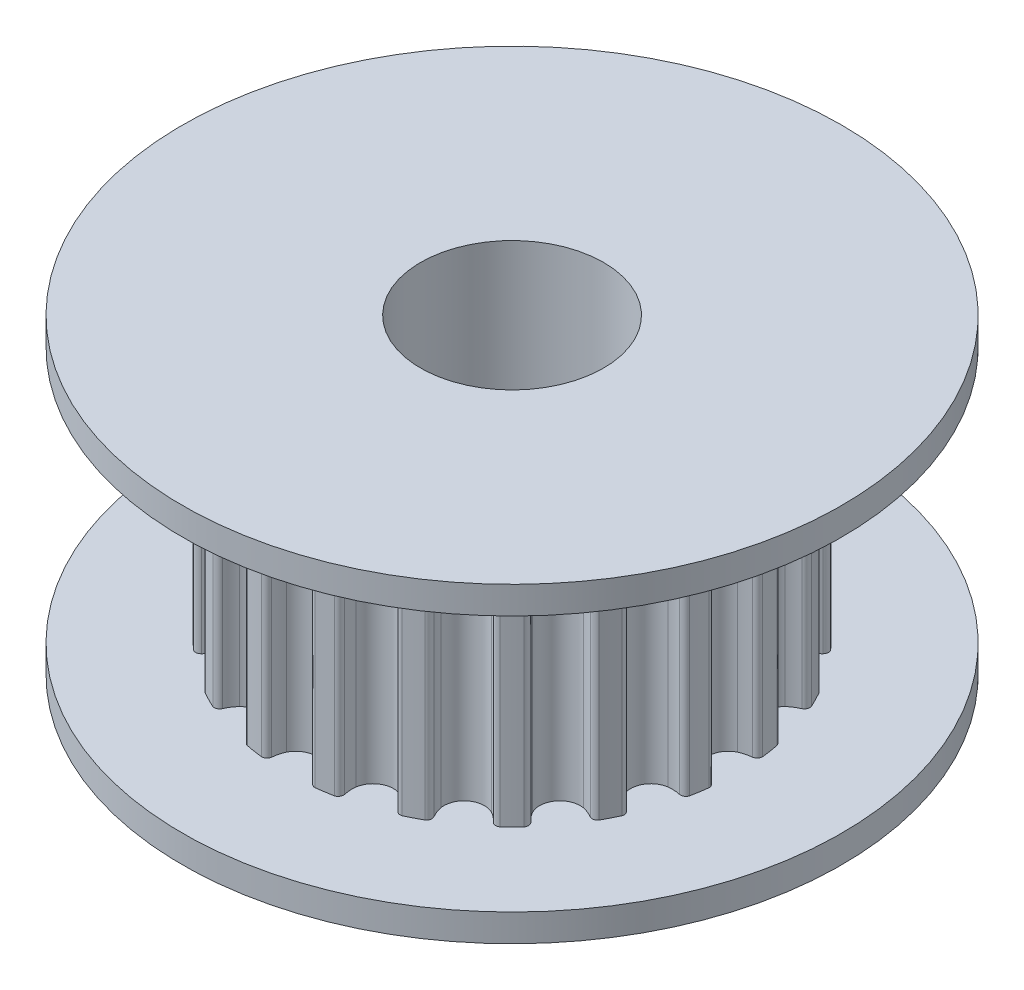
SolidWorks part; units mm, degrees
ref_plane "Front" through (0, 0, 0) normal (0, 0, 1) x (1, 0, 0)
ref_plane "Top" through (0, 0, 0) normal (0, 1, 0) x (1, 0, 0)
ref_plane "Right" through (0, 0, 0) normal (1, 0, 0) x (0, 0, -1)
sketch "Sketch1" plane through (0, 0, 0) normal (0, 0, 1) x (1, 0, 0)
  line L0 (0, 0) -> (0, 8.5) construction
  line L1 (2.5, 0) -> (2.5, 8.5)
  line L2 (2.5, 8.5) -> (9, 8.5)
  line L3 (9, 8.5) -> (9, 7.75)
  line L4 (9, 7.75) -> (6.3662, 7.75)
  line L5 (6.3662, 7.75) -> (6.3662, 0.75)
  line L6 (6.3662, 0.75) -> (9, 0.75)
  line L7 (9, 0.75) -> (9, 0)
  line L8 (9, 0) -> (2.5, 0)
  dimension "D1" = 8.5
  dimension "D2" = 7
  dimension "D3" = 18
  dimension "D4" = 12.7324
  dimension "D5" = 5
revolve "Revolve1" add sketch "Sketch1" angle 360 about L0
sketch "Sketch2" plane through (0, 0.75, 0) normal (0, 1, 0) x (1, 0, 0)
  circle A0 centre (0, 0) radius 6.3662 construction
  circle A1 centre (0, 0) radius 6.3662
  circle A3 centre (0, 0) radius 4.3662
  dimension "D1" = 2
extrude "Cut-Extrude1" cut sketch "Sketch2" along normal up to surface (7 mm away) up to face at (0, 7.75, -9)
sketch "Sketch3" plane through (0, 0.75, 0) normal (0, 1, 0) x (1, 0, 0)
  circle A0 centre (0, 0) radius 1.5
  arc A1 (6.1135, -0.7303) -> (5.9829, -0.5816) centre (5.9635, -0.7303) ccw
  arc A2 (5.659, -0.4964) -> (5.9829, -0.5816) centre (6.0717, 0.4144) ccw
  arc A3 (5.3522, 0) -> (5.659, -0.4964) centre (5.9072, 0) ccw
  arc A4 (5.659, 0.4964) -> (5.3522, 0) centre (5.9072, 0) ccw
  arc A5 (5.9829, 0.5816) -> (5.659, 0.4964) centre (6.0717, -0.4144) ccw
  arc A6 (5.9829, 0.5816) -> (6.1135, 0.7303) centre (5.9635, 0.7303) ccw
  arc A7 (6.1135, 0.7303) -> (6.0399, 1.1946) centre (0.0442, 0.007) ccw
  arc A8 (6.0399, 1.1946) -> (5.8698, 1.2957) centre (5.8973, 1.1482) ccw
  arc A9 (5.5354, 1.2766) -> (5.8698, 1.2957) centre (5.6465, 2.2704) ccw
  arc A10 (5.0902, 1.6539) -> (5.5354, 1.2766) centre (5.6181, 1.8254) ccw
  arc A11 (5.2286, 2.2208) -> (5.0902, 1.6539) centre (5.6181, 1.8254) ccw
  arc A12 (5.5103, 2.4019) -> (5.2286, 2.2208) centre (5.9026, 1.4821) ccw
  arc A13 (5.5103, 2.4019) -> (5.5886, 2.5838) centre (5.4459, 2.5374) ccw
  arc A14 (5.5886, 2.5838) -> (5.3752, 3.0025) centre (0.0399, 0.0203) ccw
  arc A15 (5.3752, 3.0025) -> (5.1821, 3.0461) centre (5.2538, 2.9144) ccw
  arc A16 (4.87, 2.9247) -> (5.1821, 3.0461) centre (4.6685, 3.9042) ccw
  arc A17 (4.33, 3.1459) -> (4.87, 2.9247) centre (4.779, 3.4722) ccw
  arc A18 (4.2864, 3.7279) -> (4.33, 3.1459) centre (4.779, 3.4722) ccw
  arc A19 (4.4984, 3.9872) -> (4.2864, 3.7279) centre (5.1557, 3.2336) ccw
  arc A20 (4.4984, 3.9872) -> (4.5166, 4.1843) centre (4.3953, 4.0961) ccw
  arc A21 (4.5166, 4.1843) -> (4.1843, 4.5166) centre (0.0317, 0.0317) ccw
  arc A22 (4.1843, 4.5166) -> (3.9872, 4.4984) centre (4.0961, 4.3953) ccw
  arc A23 (3.7279, 4.2864) -> (3.9872, 4.4984) centre (3.2336, 5.1557) ccw
  arc A24 (3.1459, 4.33) -> (3.7279, 4.2864) centre (3.4722, 4.779) ccw
  arc A25 (2.9247, 4.87) -> (3.1459, 4.33) centre (3.4722, 4.779) ccw
  arc A26 (3.0461, 5.1821) -> (2.9247, 4.87) centre (3.9042, 4.6685) ccw
  arc A27 (3.0461, 5.1821) -> (3.0025, 5.3752) centre (2.9144, 5.2538) ccw
  arc A28 (3.0025, 5.3752) -> (2.5838, 5.5886) centre (0.0203, 0.0399) ccw
  arc A29 (2.5838, 5.5886) -> (2.4019, 5.5103) centre (2.5374, 5.4459) ccw
  arc A30 (2.2208, 5.2286) -> (2.4019, 5.5103) centre (1.4821, 5.9026) ccw
  arc A31 (1.6539, 5.0902) -> (2.2208, 5.2286) centre (1.8254, 5.6181) ccw
  arc A32 (1.2766, 5.5354) -> (1.6539, 5.0902) centre (1.8254, 5.6181) ccw
  arc A33 (1.2957, 5.8698) -> (1.2766, 5.5354) centre (2.2704, 5.6465) ccw
  arc A34 (1.2957, 5.8698) -> (1.1946, 6.0399) centre (1.1482, 5.8973) ccw
  arc A35 (1.1946, 6.0399) -> (0.7303, 6.1135) centre (0.007, 0.0442) ccw
  arc A36 (0.7303, 6.1135) -> (0.5816, 5.9829) centre (0.7303, 5.9635) ccw
  arc A37 (0.4964, 5.659) -> (0.5816, 5.9829) centre (-0.4144, 6.0717) ccw
  arc A38 (0, 5.3522) -> (0.4964, 5.659) centre (0, 5.9072) ccw
  arc A39 (-0.4964, 5.659) -> (0, 5.3522) centre (0, 5.9072) ccw
  arc A40 (-0.5816, 5.9829) -> (-0.4964, 5.659) centre (0.4144, 6.0717) ccw
  arc A41 (-0.5816, 5.9829) -> (-0.7303, 6.1135) centre (-0.7303, 5.9635) ccw
  arc A42 (-0.7303, 6.1135) -> (-1.1946, 6.0399) centre (-0.007, 0.0442) ccw
  arc A43 (-1.1946, 6.0399) -> (-1.2957, 5.8698) centre (-1.1482, 5.8973) ccw
  arc A44 (-1.2766, 5.5354) -> (-1.2957, 5.8698) centre (-2.2704, 5.6465) ccw
  arc A45 (-1.6539, 5.0902) -> (-1.2766, 5.5354) centre (-1.8254, 5.6181) ccw
  arc A46 (-2.2208, 5.2286) -> (-1.6539, 5.0902) centre (-1.8254, 5.6181) ccw
  arc A47 (-2.4019, 5.5103) -> (-2.2208, 5.2286) centre (-1.4821, 5.9026) ccw
  arc A48 (-2.4019, 5.5103) -> (-2.5838, 5.5886) centre (-2.5374, 5.4459) ccw
  arc A49 (-2.5838, 5.5886) -> (-3.0025, 5.3752) centre (-0.0203, 0.0399) ccw
  arc A50 (-3.0025, 5.3752) -> (-3.0461, 5.1821) centre (-2.9144, 5.2538) ccw
  arc A51 (-2.9247, 4.87) -> (-3.0461, 5.1821) centre (-3.9042, 4.6685) ccw
  arc A52 (-3.1459, 4.33) -> (-2.9247, 4.87) centre (-3.4722, 4.779) ccw
  arc A53 (-3.7279, 4.2864) -> (-3.1459, 4.33) centre (-3.4722, 4.779) ccw
  arc A54 (-3.9872, 4.4984) -> (-3.7279, 4.2864) centre (-3.2336, 5.1557) ccw
  arc A55 (-3.9872, 4.4984) -> (-4.1843, 4.5166) centre (-4.0961, 4.3953) ccw
  arc A56 (-4.1843, 4.5166) -> (-4.5166, 4.1843) centre (-0.0317, 0.0317) ccw
  arc A57 (-4.5166, 4.1843) -> (-4.4984, 3.9872) centre (-4.3953, 4.0961) ccw
  arc A58 (-4.2864, 3.7279) -> (-4.4984, 3.9872) centre (-5.1557, 3.2336) ccw
  arc A59 (-4.33, 3.1459) -> (-4.2864, 3.7279) centre (-4.779, 3.4722) ccw
  arc A60 (-4.87, 2.9247) -> (-4.33, 3.1459) centre (-4.779, 3.4722) ccw
  arc A61 (-5.1821, 3.0461) -> (-4.87, 2.9247) centre (-4.6685, 3.9042) ccw
  arc A62 (-5.1821, 3.0461) -> (-5.3752, 3.0025) centre (-5.2538, 2.9144) ccw
  arc A63 (-5.3752, 3.0025) -> (-5.5886, 2.5838) centre (-0.0399, 0.0203) ccw
  arc A64 (-5.5886, 2.5838) -> (-5.5103, 2.4019) centre (-5.4459, 2.5374) ccw
  arc A65 (-5.2286, 2.2208) -> (-5.5103, 2.4019) centre (-5.9026, 1.4821) ccw
  arc A66 (-5.0902, 1.6539) -> (-5.2286, 2.2208) centre (-5.6181, 1.8254) ccw
  arc A67 (-5.5354, 1.2766) -> (-5.0902, 1.6539) centre (-5.6181, 1.8254) ccw
  arc A68 (-5.8698, 1.2957) -> (-5.5354, 1.2766) centre (-5.6465, 2.2704) ccw
  arc A69 (-5.8698, 1.2957) -> (-6.0399, 1.1946) centre (-5.8973, 1.1482) ccw
  arc A70 (-6.0399, 1.1946) -> (-6.1135, 0.7303) centre (-0.0442, 0.007) ccw
  arc A71 (-6.1135, 0.7303) -> (-5.9829, 0.5816) centre (-5.9635, 0.7303) ccw
  arc A72 (-5.659, 0.4964) -> (-5.9829, 0.5816) centre (-6.0717, -0.4144) ccw
  arc A73 (-5.3522, 0) -> (-5.659, 0.4964) centre (-5.9072, 0) ccw
  arc A74 (-5.659, -0.4964) -> (-5.3522, 0) centre (-5.9072, 0) ccw
  arc A75 (-5.9829, -0.5816) -> (-5.659, -0.4964) centre (-6.0717, 0.4144) ccw
  arc A76 (-5.9829, -0.5816) -> (-6.1135, -0.7303) centre (-5.9635, -0.7303) ccw
  arc A77 (-6.1135, -0.7303) -> (-6.0399, -1.1946) centre (-0.0442, -0.007) ccw
  arc A78 (-6.0399, -1.1946) -> (-5.8698, -1.2957) centre (-5.8973, -1.1482) ccw
  arc A79 (-5.5354, -1.2766) -> (-5.8698, -1.2957) centre (-5.6465, -2.2704) ccw
  arc A80 (-5.0902, -1.6539) -> (-5.5354, -1.2766) centre (-5.6181, -1.8254) ccw
  arc A81 (-5.2286, -2.2208) -> (-5.0902, -1.6539) centre (-5.6181, -1.8254) ccw
  arc A82 (-5.5103, -2.4019) -> (-5.2286, -2.2208) centre (-5.9026, -1.4821) ccw
  arc A83 (-5.5103, -2.4019) -> (-5.5886, -2.5838) centre (-5.4459, -2.5374) ccw
  arc A84 (-5.5886, -2.5838) -> (-5.3752, -3.0025) centre (-0.0399, -0.0203) ccw
  arc A85 (-5.3752, -3.0025) -> (-5.1821, -3.0461) centre (-5.2538, -2.9144) ccw
  arc A86 (-4.87, -2.9247) -> (-5.1821, -3.0461) centre (-4.6685, -3.9042) ccw
  arc A87 (-4.33, -3.1459) -> (-4.87, -2.9247) centre (-4.779, -3.4722) ccw
  arc A88 (-4.2864, -3.7279) -> (-4.33, -3.1459) centre (-4.779, -3.4722) ccw
  arc A89 (-4.4984, -3.9872) -> (-4.2864, -3.7279) centre (-5.1557, -3.2336) ccw
  arc A90 (-4.4984, -3.9872) -> (-4.5166, -4.1843) centre (-4.3953, -4.0961) ccw
  arc A91 (-4.5166, -4.1843) -> (-4.1843, -4.5166) centre (-0.0317, -0.0317) ccw
  arc A92 (-4.1843, -4.5166) -> (-3.9872, -4.4984) centre (-4.0961, -4.3953) ccw
  arc A93 (-3.7279, -4.2864) -> (-3.9872, -4.4984) centre (-3.2336, -5.1557) ccw
  arc A94 (-3.1459, -4.33) -> (-3.7279, -4.2864) centre (-3.4722, -4.779) ccw
  arc A95 (-2.9247, -4.87) -> (-3.1459, -4.33) centre (-3.4722, -4.779) ccw
  arc A96 (-3.0461, -5.1821) -> (-2.9247, -4.87) centre (-3.9042, -4.6685) ccw
  arc A97 (-3.0461, -5.1821) -> (-3.0025, -5.3752) centre (-2.9144, -5.2538) ccw
  arc A98 (-3.0025, -5.3752) -> (-2.5838, -5.5886) centre (-0.0203, -0.0399) ccw
  arc A99 (-2.5838, -5.5886) -> (-2.4019, -5.5103) centre (-2.5374, -5.4459) ccw
  arc A100 (-2.2208, -5.2286) -> (-2.4019, -5.5103) centre (-1.4821, -5.9026) ccw
  arc A101 (-1.6539, -5.0902) -> (-2.2208, -5.2286) centre (-1.8254, -5.6181) ccw
  arc A102 (-1.2766, -5.5354) -> (-1.6539, -5.0902) centre (-1.8254, -5.6181) ccw
  arc A103 (-1.2957, -5.8698) -> (-1.2766, -5.5354) centre (-2.2704, -5.6465) ccw
  arc A104 (-1.2957, -5.8698) -> (-1.1946, -6.0399) centre (-1.1482, -5.8973) ccw
  arc A105 (-1.1946, -6.0399) -> (-0.7303, -6.1135) centre (-0.007, -0.0442) ccw
  arc A106 (-0.7303, -6.1135) -> (-0.5816, -5.9829) centre (-0.7303, -5.9635) ccw
  arc A107 (-0.4964, -5.659) -> (-0.5816, -5.9829) centre (0.4144, -6.0717) ccw
  arc A108 (0, -5.3522) -> (-0.4964, -5.659) centre (0, -5.9072) ccw
  arc A109 (0.4964, -5.659) -> (0, -5.3522) centre (0, -5.9072) ccw
  arc A110 (0.5816, -5.9829) -> (0.4964, -5.659) centre (-0.4144, -6.0717) ccw
  arc A111 (0.5816, -5.9829) -> (0.7303, -6.1135) centre (0.7303, -5.9635) ccw
  arc A112 (0.7303, -6.1135) -> (1.1946, -6.0399) centre (0.007, -0.0442) ccw
  arc A113 (1.1946, -6.0399) -> (1.2957, -5.8698) centre (1.1482, -5.8973) ccw
  arc A114 (1.2766, -5.5354) -> (1.2957, -5.8698) centre (2.2704, -5.6465) ccw
  arc A115 (1.6539, -5.0902) -> (1.2766, -5.5354) centre (1.8254, -5.6181) ccw
  arc A116 (2.2208, -5.2286) -> (1.6539, -5.0902) centre (1.8254, -5.6181) ccw
  arc A117 (2.4019, -5.5103) -> (2.2208, -5.2286) centre (1.4821, -5.9026) ccw
  arc A118 (2.4019, -5.5103) -> (2.5838, -5.5886) centre (2.5374, -5.4459) ccw
  arc A119 (2.5838, -5.5886) -> (3.0025, -5.3752) centre (0.0203, -0.0399) ccw
  arc A120 (3.0025, -5.3752) -> (3.0461, -5.1821) centre (2.9144, -5.2538) ccw
  arc A121 (2.9247, -4.87) -> (3.0461, -5.1821) centre (3.9042, -4.6685) ccw
  arc A122 (3.1459, -4.33) -> (2.9247, -4.87) centre (3.4722, -4.779) ccw
  arc A123 (3.7279, -4.2864) -> (3.1459, -4.33) centre (3.4722, -4.779) ccw
  arc A124 (3.9872, -4.4984) -> (3.7279, -4.2864) centre (3.2336, -5.1557) ccw
  arc A125 (3.9872, -4.4984) -> (4.1843, -4.5166) centre (4.0961, -4.3953) ccw
  arc A126 (4.1843, -4.5166) -> (4.5166, -4.1843) centre (0.0317, -0.0317) ccw
  arc A127 (4.5166, -4.1843) -> (4.4984, -3.9872) centre (4.3953, -4.0961) ccw
  arc A128 (4.2864, -3.7279) -> (4.4984, -3.9872) centre (5.1557, -3.2336) ccw
  arc A129 (4.33, -3.1459) -> (4.2864, -3.7279) centre (4.779, -3.4722) ccw
  arc A130 (4.87, -2.9247) -> (4.33, -3.1459) centre (4.779, -3.4722) ccw
  arc A131 (5.1821, -3.0461) -> (4.87, -2.9247) centre (4.6685, -3.9042) ccw
  arc A132 (5.1821, -3.0461) -> (5.3752, -3.0025) centre (5.2538, -2.9144) ccw
  arc A133 (5.3752, -3.0025) -> (5.5886, -2.5838) centre (0.0399, -0.0203) ccw
  arc A134 (5.5886, -2.5838) -> (5.5103, -2.4019) centre (5.4459, -2.5374) ccw
  arc A135 (5.2286, -2.2208) -> (5.5103, -2.4019) centre (5.9026, -1.4821) ccw
  arc A136 (5.0902, -1.6539) -> (5.2286, -2.2208) centre (5.6181, -1.8254) ccw
  arc A137 (5.5354, -1.2766) -> (5.0902, -1.6539) centre (5.6181, -1.8254) ccw
  arc A138 (5.8698, -1.2957) -> (5.5354, -1.2766) centre (5.6465, -2.2704) ccw
  arc A139 (5.8698, -1.2957) -> (6.0399, -1.1946) centre (5.8973, -1.1482) ccw
  arc A140 (6.0399, -1.1946) -> (6.1135, -0.7303) centre (0.0442, -0.007) ccw
  circle A141 centre (0, 0) radius 4.3662 construction
  circle A142 centre (0, 0) radius 4.3662
extrude "Boss-Extrude1" add sketch "Sketch3" along normal up to surface (7 mm away) contours A139 A140 A1 A2 A3 A4 A5 A6 A7 A8 A9 A10 A11 A12 A13 A14 A15 A16 A17 A18 A19 A20 A21 A22 A23 A24 A25 A26 A27 A28 A29 A30 A31 A32 A33 A34 A35 A36 A37 A38 A39 A40 A41 A42 A43 A44 A45 A46 A47 A48 A49
equation "\"D4@Sketch1\"=20*2/3.14159"
